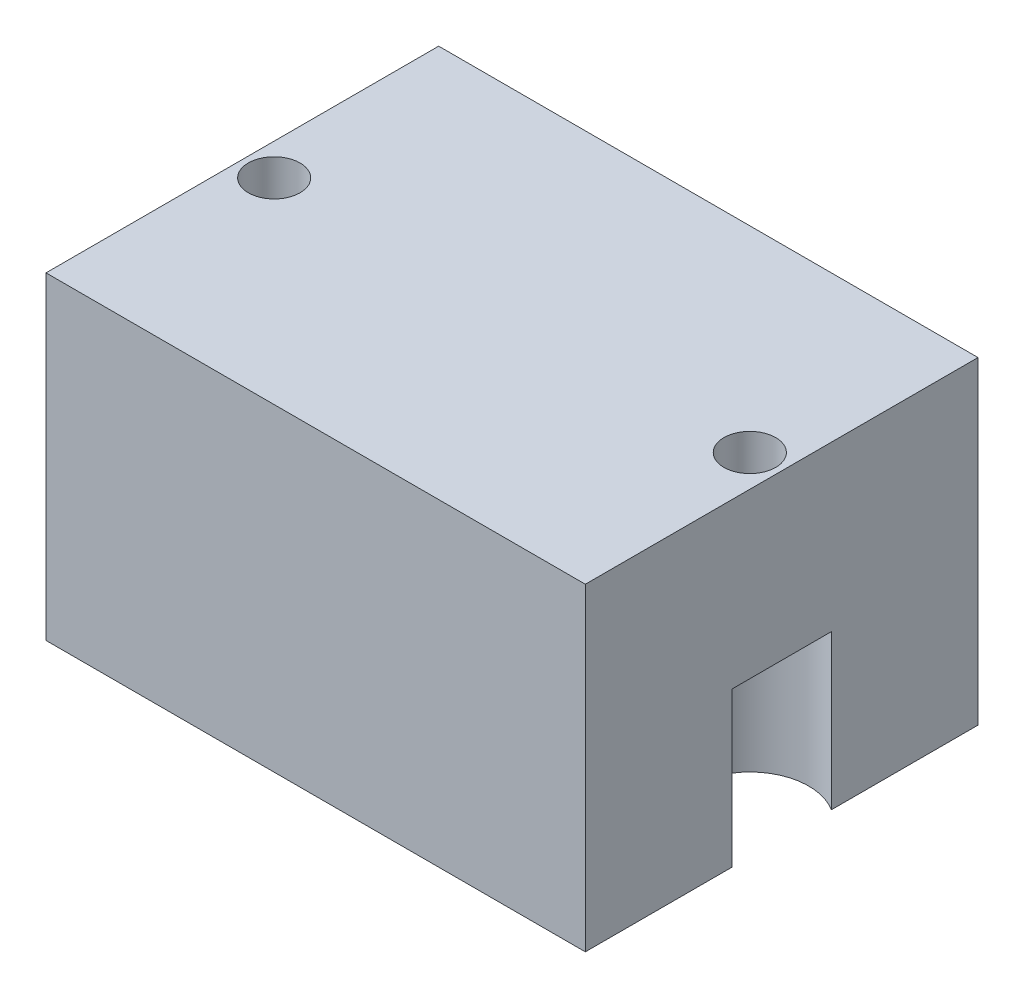
SolidWorks part; units mm, degrees
ref_plane "Front Plane" through (0, 0, 0) normal (0, 0, 1) x (1, 0, 0)
ref_plane "Top Plane" through (0, 0, 0) normal (0, 1, 0) x (1, 0, 0)
ref_plane "Right Plane" through (0, 0, 0) normal (1, 0, 0) x (0, 0, -1)
sketch "Sketch1" plane through (0, 0, 0) normal (0, 1, 0) x (1, 0, 0)
  line L1 (0, 0) -> (25.41, 0)
  line L2 (0, 0) -> (0, 18.5)
  line L3 (0, 18.5) -> (25.41, 18.5)
  line L4 (25.41, 0) -> (25.41, 18.5)
extrude "Boss-Extrude1" add sketch "Sketch1" along normal blind 15
sketch "Sketch2" plane through (0, 0, 0) normal (0, -1, 0) x (1, 0, 0)
  line L0 (0, 0) -> (1.5, 0)
  line L1 (0, 0) -> (25.41, 0) construction
  line L2 (1.5, 0) -> (1.5, -18.5)
  line L3 (25.41, -18.5) -> (0, -18.5) construction
  line L4 (25.41, 0) -> (23.91, 0)
  line L5 (23.91, 0) -> (23.91, -18.5)
  line L6 (0, 0) -> (0, -1.5)
  line L7 (0, -18.5) -> (0, 0) construction
  line L8 (0, -1.5) -> (25.41, -1.5)
  line L9 (25.41, 0) -> (25.41, -18.5) construction
  line L10 (0, -18.5) -> (0, -17)
  line L11 (0, -17) -> (25.41, -17)
hole_wizard "#2-56 Tapped Hole1" positions "Sketch3" profile "Sketch4" tap size "#2-56" standard "ANSI Inch"
sketch "Sketch3" plane through (0, 0, 0) normal (0, -1, 0) x (-1, 0, 0)
  line L0 (-23.91, 0) -> (-23.91, 18.5) construction
  line L1 (0, 17) -> (-25.41, 17) construction
  line L2 (0, 1.5) -> (-25.41, 1.5) construction
  line L3 (-1.5, 0) -> (-1.5, 18.5) construction
  point P0 (-23.91, 17)
  point P6 (-23.91, 1.5)
  point P10 (-1.5, 1.5)
  point P14 (-1.5, 17)
sketch "Sketch4" plane through (23.91, 0, -17) normal (1, 0, 0) x (0, 0, -1)
  line L0 (0, 0) -> (0, 8)
  line L1 (0, 8) -> (0.889, 7.4658)
  line L2 (0.889, 7.4658) -> (0.889, 0)
  line L5 (0.889, 0) -> (0, 0)
  line L10 (0, 8) -> (-0.889, 7.4658) construction
  line L11 (0, -6.35) -> (0, 107.95) construction
  dimension "Tap Drill Dia." = 1.778
  dimension "Tap Drill Depth" = 8
  dimension "Drill Angle" = 118
cosmetic thread "Hole Thread1" parameters "D1"=4.37, "D2"=2.1844
cosmetic thread "Hole Thread2" parameters "D1"=4.37, "D2"=2.1844
cosmetic thread "Hole Thread3" parameters "D1"=4.37, "D2"=2.1844
cosmetic thread "Hole Thread4" parameters "D1"=4.37, "D2"=2.1844
sketch "Sketch5" plane through (0, 0, 0) normal (0, -1, 0) x (1, 0, 0)
  circle A0 centre (12.705, -9.25) radius 3
extrude "Cut-Extrude1" cut sketch "Sketch5" against normal blind 3
sketch "Sketch6" plane through (0, 0, 0) normal (0, -1, 0) x (1, 0, 0)
  line L0 (0, -9.25) -> (25.41, -9.25)
  line L1 (0, -18.5) -> (0, 0) construction
  line L2 (25.41, 0) -> (25.41, -18.5) construction
  line L3 (0, -9.25) -> (5, -9.25)
  line L4 (25.41, -9.25) -> (20.41, -9.25)
sketch "Sketch11" plane through (0, 0, 0) normal (0, -1, 0) x (1, 0, 0)
  line L0 (12.705, 0) -> (12.705, -18.5)
  line L1 (0, 0) -> (25.41, 0) construction
  line L2 (25.41, -18.5) -> (0, -18.5) construction
  line L3 (12.705, -18.5) -> (12.705, -17)
  line L4 (12.705, 0) -> (12.705, -1.5)
sketch "Sketch12" plane through (0, 0, 0) normal (0, -1, 0) x (1, 0, 0)
  line L0 (1.5, -1.5) -> (1.5, -17)
  line L1 (23.91, -1.5) -> (23.91, -17)
  line L2 (0, -9.25) -> (1.5, -9.25)
  line L3 (0, -18.5) -> (0, 0) construction
  line L4 (25.41, -9.25) -> (23.91, -9.25)
  line L5 (25.41, 0) -> (25.41, -18.5) construction
hole_wizard "CBORE for #2 Binding Head Machine Screw1" positions "Sketch13" profile "Sketch14" counterbore size "#2" standard "ANSI Inch" end condition through all
sketch "Sketch13" plane through (0, 0, 0) normal (0, -1, 0) x (-1, 0, 0)
  point P0 (-23.91, 9.25)
  point P3 (-1.5, 9.25)
sketch "Sketch14" plane through (23.91, 0, -9.25) normal (1, 0, 0) x (0, 0, -1)
  line L0 (0, 0) -> (0, 15)
  line L1 (0, 15) -> (1.2192, 15)
  line L3 (1.2192, 15) -> (1.2192, 7.27)
  line L4 (1.2192, 7.27) -> (2.7788, 7.27)
  line L5 (2.7788, 7.27) -> (2.7788, 0)
  line L7 (2.7788, 0) -> (0, 0)
  line L11 (0, -6.35) -> (0, 107.95) construction
  dimension "Thru Hole Dia." = 2.4384
  dimension "Thru Hole Depth" = 15
  dimension "C'Bore Dia." = 5.5575
  dimension "C'Bore Depth" = 7.27
